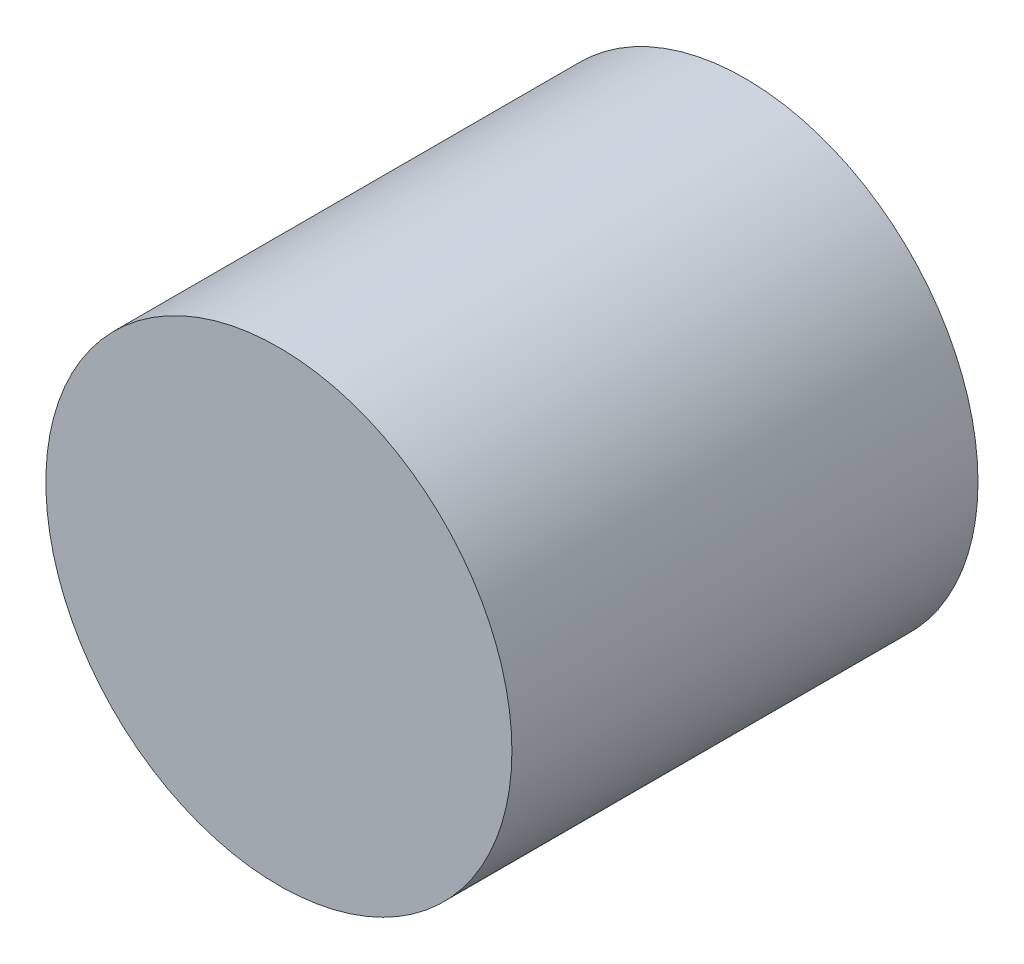
SolidWorks part; units mm, degrees
ref_plane "Front Plane" through (0, 0, 0) normal (0, 0, 1) x (1, 0, 0)
ref_plane "Top Plane" through (0, 0, 0) normal (0, 1, 0) x (1, 0, 0)
ref_plane "Right Plane" through (0, 0, 0) normal (1, 0, 0) x (0, 0, -1)
sketch "Sketch1" plane through (0, 0, 0) normal (0, 0, 1) x (1, 0, 0)
  circle A0 centre (0, 0) radius 1.5
extrude "Boss-Extrude1" add sketch "Sketch1" along normal blind 3
